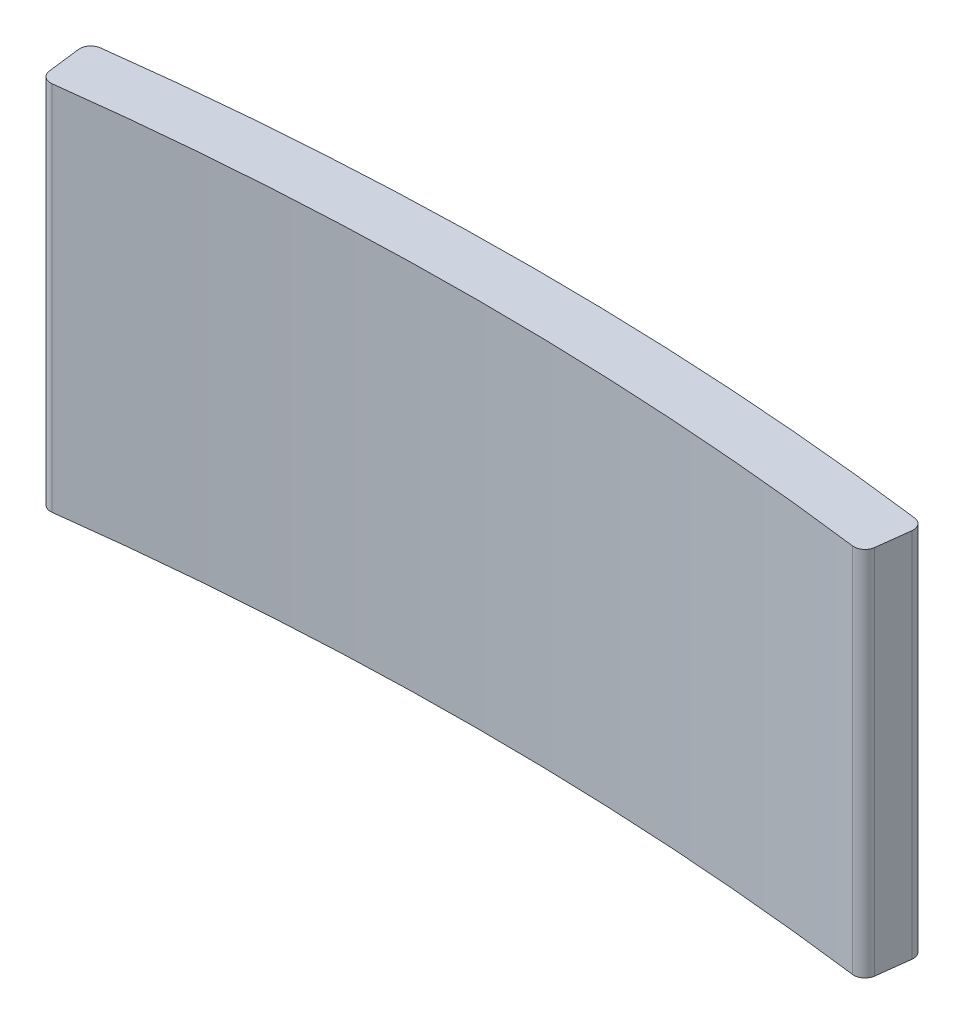
SolidWorks part; units mm, degrees
ref_plane "Plano frontal" through (0, 0, 0) normal (0, 0, 1) x (1, 0, 0)
ref_plane "Plano superior" through (0, 0, 0) normal (0, 1, 0) x (1, 0, 0)
ref_plane "Plano direito" through (0, 0, 0) normal (1, 0, 0) x (0, 0, -1)
sketch "Esboço1" plane through (0, 0, 0) normal (0, 1, 0) x (1, 0, 0)
  line L0 (0, 123.3708) -> (0, -121.2751) construction
  line L1 (11.08, 84.2747) -> (11.2628, 85.7636)
  line L2 (-11.0811, 84.2746) -> (-11.2639, 85.7635)
  arc A0 (11.08, 84.2747) -> (-11.0811, 84.2746) centre (0, 0) ccw
  arc A2 (11.2628, 85.7636) -> (-11.2639, 85.7635) centre (0, 0) ccw
  dimension "D1" = 7
  dimension "D3" = 170
  dimension "D4" = 173
  dimension "D2" = 7
extrude "Ressalto-extrusão2" add sketch "Esboço1" along normal blind 10
fillet "Filete1" radius 0.3 4 edges at (11.2628, 5, -85.7636) (11.08, 5, -84.2747) (-11.0811, 5, -84.2746) (-11.2639, 5, -85.7635)
